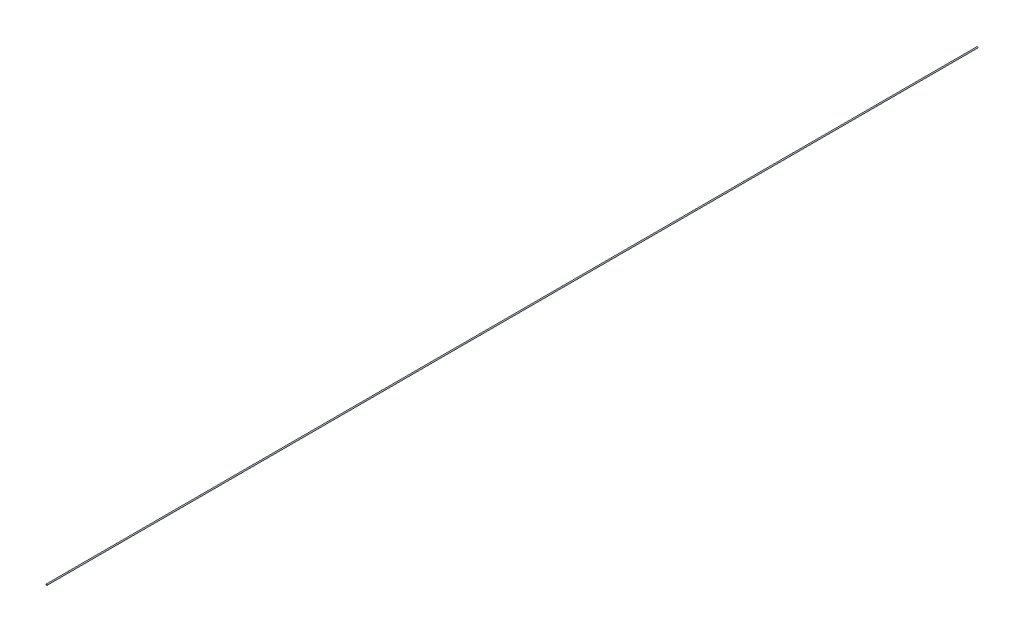
SolidWorks part; units mm, degrees
ref_plane "Front" through (0, 0, 0) normal (0, 0, 1) x (1, 0, 0)
ref_plane "Top" through (0, 0, 0) normal (0, 1, 0) x (1, 0, 0)
ref_plane "Right" through (0, 0, 0) normal (1, 0, 0) x (0, 0, -1)
sketch "Sketch1" plane through (0, 0, 0) normal (0, 0, 1) x (1, 0, 0)
  circle A0 centre (0, 0) radius 0.25
  dimension "D1" = 0.5
sketch "Sketch2" plane through (0, 0, 0) normal (0, 1, 0) x (1, 0, 0)
  line L0 (0, 0) -> (0, 400)
  dimension "D1" = 400
sweep "Sweep1" add profiles "Sketch1" path "Sketch2"
